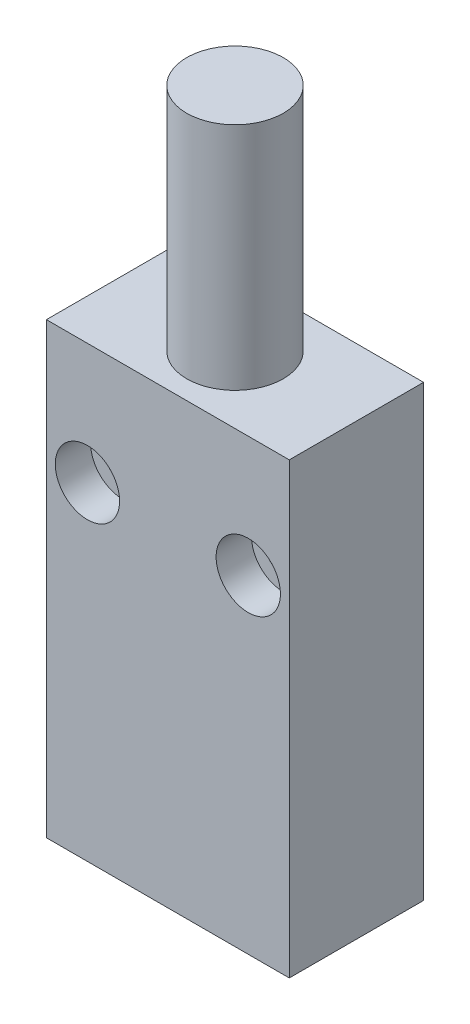
SolidWorks part; units mm, degrees
ref_plane "Front Plane" through (0, 0, 0) normal (0, 0, 1) x (1, 0, 0)
ref_plane "Top Plane" through (0, 0, 0) normal (0, 1, 0) x (1, 0, 0)
ref_plane "Right Plane" through (0, 0, 0) normal (1, 0, 0) x (0, 0, -1)
sketch "Sketch1" plane through (0, 0, 0) normal (0, 0, 1) x (1, 0, 0)
  line L1 (15.1, -27.9) -> (-15.1, -27.9)
  line L2 (15.1, -27.9) -> (15.1, 27.9)
  line L3 (15.1, 27.9) -> (-15.1, 27.9)
  line L4 (-15.1, -27.9) -> (-15.1, 27.9)
  line L5 (15.1, -27.9) -> (-15.1, 27.9) construction
  line L6 (15.1, 27.9) -> (-15.1, -27.9) construction
  point P0 (0, 0)
  dimension "D1" = 55.8
  dimension "D2" = 30.2
extrude "Boss-Extrude1" add sketch "Sketch1" along normal mid plane 16.7
hole_wizard "CBORE for M4 Hex Socket Head Cap Screw1" positions "Sketch2" profile "Sketch3" counterbore size "M4" standard "ISO" end condition through all
sketch "Sketch2" plane through (0, 0, 8.35) normal (0, 0, 1) x (1, 0, 0)
  line L0 (0, 0) -> (0, 12.9) construction
  line L1 (0, 12.9) -> (-10, 12.9) construction
  line L3 (0, 12.9) -> (10, 12.9) construction
  line L5 (-15.1, -27.9) -> (15.1, -27.9) construction
  point P0 (-10, 12.9)
  point P2 (10, 12.9)
  dimension "D1" = 10
  dimension "D2" = 40.8
sketch "Sketch3" plane through (-10, 12.9, 8.35) normal (1, 0, 0) x (0, -1, 0)
  line L0 (0, 0) -> (0, 16.7)
  line L1 (0, 16.7) -> (2.25, 16.7)
  line L3 (2.25, 16.7) -> (2.25, 4.4)
  line L4 (2.25, 4.4) -> (4, 4.4)
  line L5 (4, 4.4) -> (4, 0)
  line L7 (4, 0) -> (0, 0)
  line L11 (0, -6.35) -> (0, 107.95) construction
  dimension "Thru Hole Dia." = 4.5
  dimension "Thru Hole Depth" = 16.7
  dimension "C'Bore Dia." = 8
  dimension "C'Bore Depth" = 4.4
ref_plane "Plane1" through (0, 12.9, 0) normal (0, 1, 0) x (1, 0, 0)
sketch "Sketch4" plane through (0, 27.9, 0) normal (0, 1, 0) x (1, 0, 0)
  circle A0 centre (0, 0) radius 6
  dimension "D1" = 12
extrude "Boss-Extrude2" add sketch "Sketch4" along normal blind 43.6 from surface at -15 starting at plane "Plane1"
